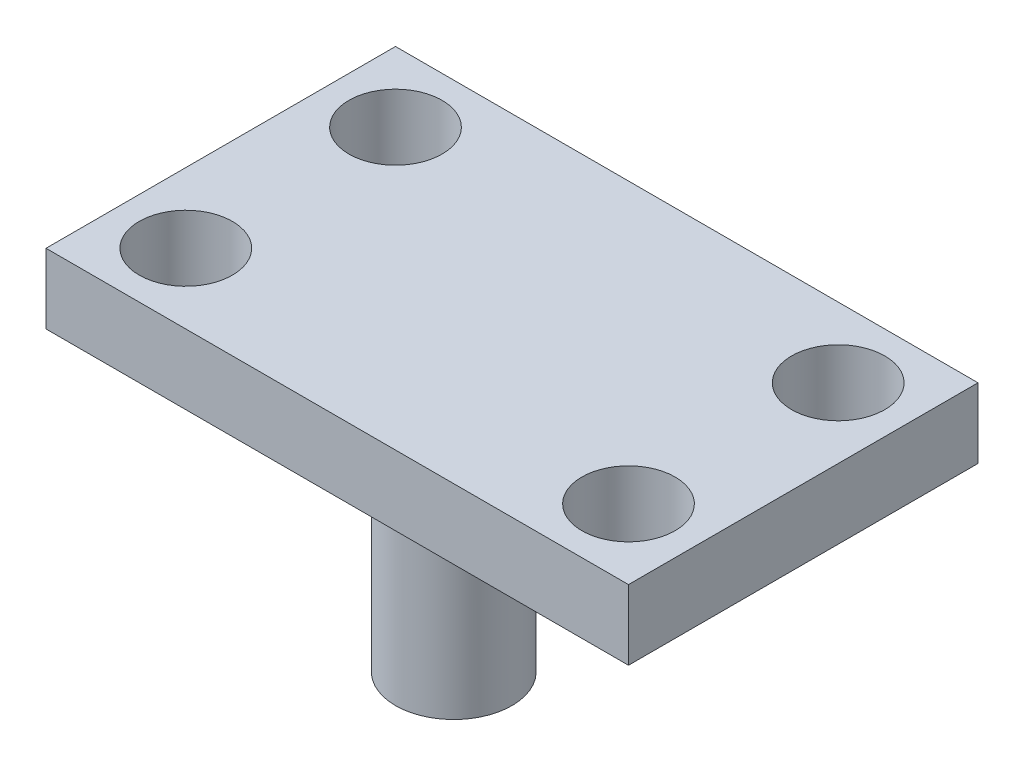
SolidWorks part; units mm, degrees
ref_plane "Front Plane" through (0, 0, 0) normal (0, 0, 1) x (1, 0, 0)
ref_plane "Top Plane" through (0, 0, 0) normal (0, 1, 0) x (1, 0, 0)
ref_plane "Right Plane" through (0, 0, 0) normal (1, 0, 0) x (0, 0, -1)
sketch "Sketch1" plane through (0, 0, 0) normal (0, 1, 0) x (1, 0, 0)
  line L0 (125, -60.9533) -> (125, 252.5879) construction
  line L1 (0, 0) -> (250, 0)
  line L2 (0, 0) -> (0, 150)
  line L3 (0, 150) -> (250, 150)
  line L4 (250, 0) -> (250, 150)
  circle A0 centre (30, 120) radius 20
  circle A1 centre (30, 30) radius 20
  circle A2 centre (220, 120) radius 20
  circle A3 centre (220, 30) radius 20
  point P15 (0, 0)
  point P16 (0, 0)
  point P17 (0, 0)
  dimension "D3" = 40
  dimension "D1" = 250
  dimension "D2" = 150
  dimension "D4" = 30
  dimension "D5" = 30
  dimension "D6" = 90
extrude "Boss-Extrude1" add sketch "Sketch1" along normal blind 30
sketch "Sketch2" plane through (0, 30, 0) normal (0, 1, 0) x (1, 0, 0)
  line L0 (250, 0) -> (250, 150) construction
  line L1 (250, 150) -> (0, 150) construction
  circle A0 centre (125, 50) radius 25
  dimension "D1" = 125
  dimension "D3" = 50
  dimension "D2" = 100
extrude "Boss-Extrude2" add sketch "Sketch2" against normal blind 120
